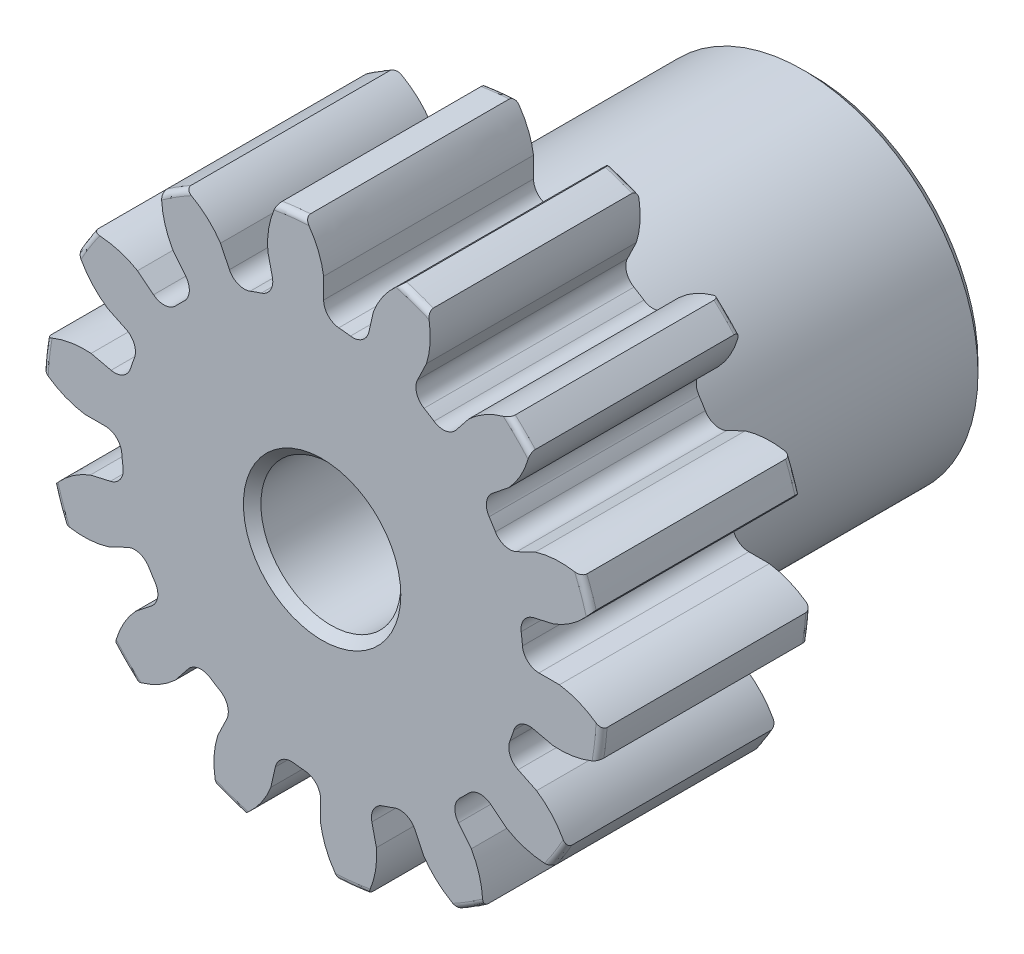
SolidWorks part; units mm, degrees
ref_plane "Front" through (0, 0, 0) normal (0, 0, 1) x (1, 0, 0)
ref_plane "Top" through (0, 0, 0) normal (0, 1, 0) x (1, 0, 0)
ref_plane "Right" through (0, 0, 0) normal (1, 0, 0) x (0, 0, -1)
sketch "Sketch1" plane through (0, 0, 0) normal (0, 0, 1) x (1, 0, 0)
  line L0 (-177.8, 0) -> (177.8, 0) construction
  circle A0 centre (0, 0) radius 6.35
  circle A1 centre (0, 0) radius 5.5626 construction
  circle A3 centre (0, 0) radius 4.562 construction
  dimension "D1" = 1.788
  dimension "OD" = 12.7
  dimension "Ptich Dia" = 11.1252
  dimension "Root Dia" = 9.124
  dimension "D3" = 0.7874
  dimension "Number of Teeth" = 355.6
extrude "Boss-Extrude1" add sketch "Sketch1" against normal blind 4.7625
sketch "Sketch2" plane through (0, 0, 0) normal (1, 0, 0) x (0, 0, -1)
  line L0 (4.7625, 0) -> (11.1125, 0)
  line L1 (4.7625, 0) -> (4.7625, 3.9688)
  line L2 (4.7625, 3.9688) -> (11.1125, 3.9688)
  line L3 (11.1125, 3.9688) -> (11.1125, 0)
  point P5 (11.1125, -3.9688)
  point P6 (0, -6.35)
  point P7 (4.7625, -6.35)
  point P9 (0, 6.35)
  dimension "Face Wd" = 4.7625
  dimension "B Hub Dia" = 7.9375
  dimension "D O'all Lg." = 11.1125
revolve "Revolve1" add sketch "Sketch2" angle 360 about L0
fillet "Fillet2" radius 0.127 3 edges at (6.35, 0, -4.7625) (6.35, 0, 0) (3.9688, 0, -4.7625)
sketch "Sketch3" plane through (0, 0, 0) normal (0, 0, 1) x (1, 0, 0)
  line L0 (0, 0) -> (0, 6.35) construction
  line L1 (-1.3484, 5.2139) -> (0, 5.5626)
  line L2 (-9.5921, 5.5626) -> (9.5921, 5.5626) construction
  line L3 (-9.2865, 3.1609) -> (9.2865, 7.9643) construction
  line L4 (-1.3484, 5.2139) -> (0, 0) construction
  line L5 (-3.4393, 4.1441) -> (0, 0) construction
  line L6 (-3.4393, 4.1441) -> (-0.5651, 6.5295) construction
  line L7 (-0.9402, 5.3027) -> (0, 0) construction
  line L8 (-0.9402, 5.3027) -> (0.0197, 5.4729) construction
  arc A0 (-1.3484, 5.2139) -> (-3.4393, 4.1441) centre (0, 0) ccw
  circle A1 centre (0, 0) radius 5.5626 construction
  circle A2 centre (0, 0) radius 5.3854 construction
  arc A3 (-1.3484, 5.2139) -> (-0.9402, 5.3027) centre (0, 0) cw
  circle A4 centre (0, 0) radius 6.35 construction
  point P6 (0, 5.5626)
  dimension "D1" = 1.3928
  dimension "Pressure Angle" = 14.5
  dimension "D2" = 2.3677
  dimension "D3" = 3.7351
  dimension "D4" = 0.4178
  dimension "D5" = 0.9749
sketch "Sketch4" plane through (0, 0, 0) normal (0, 0, 1) x (1, 0, 0)
  line L0 (0, 0) -> (0.6189, 5.4929) construction
  line L1 (0.0348, 5.3853) -> (0.0348, 4.5619)
  line L2 (0, 5.5626) -> (1.2378, 5.4231) construction
  line L3 (1.1644, 5.258) -> (0.9812, 4.4553)
  line L4 (0.0348, 4.5619) -> (0, 0) construction
  line L5 (0, 0) -> (0, 6.35) construction
  line L6 (-3.4393, 4.1441) -> (-0.5651, 6.5295) construction
  line L7 (-3.4393, 4.1441) -> (-0.5651, 6.5295) construction
  arc A0 (0.9812, 4.4553) -> (0.0348, 4.5619) centre (0, 0) ccw
  arc A1 (0, 5.5626) -> (1.2378, 5.4231) centre (0, 0) cw construction
  circle A2 centre (0, 0) radius 5.5626 construction
  circle A3 centre (0, 0) radius 5.3854 construction
  circle A4 centre (0, 0) radius 4.562 construction
  arc A5 (2.0039, 6.24) -> (-0.5651, 6.5295) centre (0, 0) ccw
  spline S0 degree 2 poles (-0.5651, 6.5295) (-0.061, 6.0291) (0.0348, 5.3853) knots 0 0 0 1 1 1
  spline S1 degree 2 poles (2.0039, 6.24) (1.4011, 5.8644) (1.1644, 5.258) knots 0 0 0 1 1 1
  dimension "D1" = 1.2482
extrude "Cut-Extrude1" cut sketch "Sketch4" against normal through all
fillet "Fillet1" radius 0.3745 2 edges at (0.9812, 4.4553, -2.3813) (0.0348, 4.5619, -2.3813)
pattern_circular "CirPattern1" count 14 over 360 about axis through (0, 0, -4.7625) along (0, 0, 1) of "Cut-Extrude1", "Fillet1"
sketch "Sketch5" plane through (0, 0, 0) normal (0, 0, 1) x (1, 0, 0)
  circle A0 centre (0, 0) radius 1.5875
  circle A1 centre (0, 0) radius 1.5875 construction
  dimension "Bore Min" = 3.175
  dimension "Bore Max" = 3.175
extrude "Cut-Extrude2" cut sketch "Sketch5" against normal through all
chamfer "Chamfer1" distance 0.1984 angle 45 3 edges at (3.9688, 0, -11.1125) (1.5875, 0, 0) (1.5875, 0, -11.1125)
sketch "Pitch Dia" plane through (0, 0, 0) normal (0, 0, 1) x (1, 0, 0)
  circle A0 centre (0, 0) radius 5.5626 construction
  circle A1 centre (0, 0) radius 5.5626 construction
equation "\"D1@Boss-Extrude1\" = \"Face Wd@Sketch2\""
equation "\"D2@Sketch3\" = \"D1@Sketch3\"*1.7"
equation "\"D3@Sketch3\" = \"D1@Sketch3\"+\"D2@Sketch3\"-.001"
equation "\"D4@Sketch3\" = \"D1@Sketch3\"*.3"
equation "\"D5@Sketch3\" = \"D1@Sketch3\"-\"D4@Sketch3\""
equation "\"D1@Sketch4\" = 1.5708/(\"Number of Teeth@Sketch1\"/\"Ptich Dia@Sketch1\")"
equation "\"D1@Chamfer1\" = \"B Hub Dia@Sketch2\"*.025"
equation "\"D1@CirPattern1\" = \"Number of Teeth@Sketch1\""
equation "\"D1@Fillet1\" = \"D1@Sketch4\"*.3"
equation "\"D1@Fillet2\" = \"OD@Sketch1\"*.01"
equation "\"D1@Sketch1\" = 2.250/(\"Number of Teeth@Sketch1\"/\"Ptich Dia@Sketch1\")"
